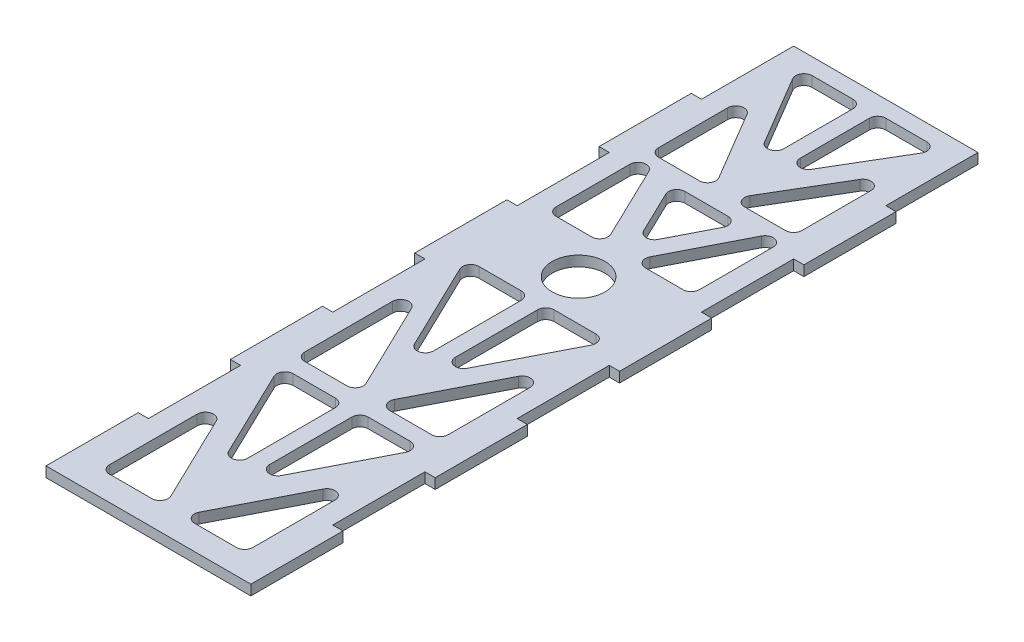
SolidWorks part; units mm, degrees
material "Balsa"
ref_plane "Front Plane" through (0, 0, 0) normal (0, 0, 1) x (1, 0, 0)
ref_plane "Top Plane" through (0, 0, 0) normal (0, 1, 0) x (1, 0, 0)
ref_plane "Right Plane" through (0, 0, 0) normal (1, 0, 0) x (0, 0, -1)
sketch "Sketch1" plane through (0, -9.7437, 0) normal (0, 1, 0) x (1, 0, 0)
  line L0 (-31.75, 143.1759) -> (-28.575, 143.1759)
  line L1 (-28.575, 143.1759) -> (-28.575, 171.7509)
  line L2 (-28.575, 171.7509) -> (28.575, 171.7509)
  line L3 (28.575, 171.7509) -> (28.575, 143.1759)
  line L4 (28.575, 143.1759) -> (31.75, 143.1759)
  line L5 (31.75, 143.1759) -> (31.75, 114.6009)
  line L6 (31.75, 114.6009) -> (28.575, 114.6009)
  line L7 (28.575, 114.6009) -> (28.575, 86.0259)
  line L8 (28.575, 86.0259) -> (31.75, 86.0259)
  line L9 (31.75, 86.0259) -> (31.75, 57.4509)
  line L10 (31.75, 57.4509) -> (28.575, 57.4509)
  line L11 (28.575, 57.4509) -> (28.575, 28.8759)
  line L12 (28.575, 28.8759) -> (31.75, 28.8759)
  line L13 (31.75, 28.8759) -> (31.75, 0.3009)
  line L14 (31.75, 0.3009) -> (28.575, 0.3009)
  line L15 (28.575, 0.3009) -> (28.575, -28.2741)
  line L16 (28.575, -28.2741) -> (31.75, -28.2741)
  line L17 (31.75, -28.2741) -> (31.75, -56.8491)
  line L18 (31.75, -56.8491) -> (-31.75, -56.8491)
  line L19 (-31.75, -56.8491) -> (-31.75, -28.2741)
  line L20 (-31.75, -28.2741) -> (-28.575, -28.2741)
  line L21 (-28.575, -28.2741) -> (-28.575, 0.3009)
  line L22 (-28.575, 0.3009) -> (-31.75, 0.3009)
  line L23 (-31.75, 0.3009) -> (-31.75, 28.8759)
  line L24 (-31.75, 28.8759) -> (-28.575, 28.8759)
  line L25 (-28.575, 28.8759) -> (-28.575, 57.4509)
  line L26 (-28.575, 57.4509) -> (-31.75, 57.4509)
  line L27 (-31.75, 57.4509) -> (-31.75, 86.0259)
  line L28 (-31.75, 86.0259) -> (-28.575, 86.0259)
  line L29 (-28.575, 86.0259) -> (-28.575, 114.6009)
  line L30 (-28.575, 114.6009) -> (-31.75, 114.6009)
  line L31 (-31.75, 114.6009) -> (-31.75, 143.1759)
  line L71 (-17.7698, 166.6709) -> (-5.08, 166.6709)
  line L78 (-2.54, 164.1309) -> (-2.54, 142.6938)
  line L82 (-7.2658, 141.3999) -> (-19.9555, 162.837)
  line L83 (2.54, 164.1309) -> (2.54, 142.6938)
  line L84 (7.2658, 141.3999) -> (19.9555, 162.837)
  line L85 (17.7698, 166.6709) -> (5.08, 166.6709)
  line L86 (-22.225, 144.9279) -> (-22.225, 123.4909)
  line L87 (-19.685, 120.9509) -> (-6.9952, 120.9509)
  line L88 (-4.8095, 124.7847) -> (-17.4992, 146.2218)
  line L89 (4.8095, 124.7847) -> (17.4992, 146.2218)
  line L90 (22.225, 144.9279) -> (22.225, 123.4909)
  line L91 (19.685, 120.9509) -> (6.9952, 120.9509)
  line L98 (5.7498, 92.896) -> (17.4229, 115.756)
  line L99 (22.225, 114.6009) -> (22.225, 91.7409)
  line L100 (19.685, 89.2009) -> (8.0119, 89.2009)
  line L101 (-6.3727, 92.8442) -> (-17.3972, 115.7042)
  line L102 (-22.225, 114.6009) -> (-22.225, 91.7409)
  line L103 (-19.685, 89.2009) -> (-8.6606, 89.2009)
  line L104 (5.08, 63.8009) -> (18.076, 63.8009)
  line L105 (20.3381, 60.1057) -> (7.3421, 34.655)
  line L106 (2.54, 35.8101) -> (2.54, 61.2609)
  line L107 (-5.08, 63.8009) -> (-18.1801, 63.8009)
  line L108 (-20.468, 60.1575) -> (-7.3678, 32.9934)
  line L109 (-2.54, 34.0967) -> (-2.54, 61.2609)
  line L110 (17.4229, 40.4336) -> (4.4269, 14.9828)
  line L111 (6.689, 11.2877) -> (19.685, 11.2877)
  line L112 (22.225, 13.8277) -> (22.225, 39.2785)
  line L113 (-22.225, 40.9919) -> (-22.225, 13.8277)
  line L114 (-19.685, 11.2877) -> (-6.5849, 11.2877)
  line L115 (-4.297, 14.931) -> (-17.3972, 42.0952)
  line L116 (-18.1801, 6.2077) -> (-5.08, 6.2077)
  line L117 (-2.54, 3.6677) -> (-2.54, -23.4964)
  line L118 (-7.3678, -24.5998) -> (-20.468, 2.5644)
  line L122 (2.54, 3.6677) -> (2.54, -21.7831)
  line L123 (7.3421, -22.9382) -> (20.3381, 2.5126)
  line L124 (18.076, 6.2077) -> (5.08, 6.2077)
  line L131 (4.4269, -45.534) -> (17.4229, -20.0833)
  line L132 (22.225, -21.2384) -> (22.225, -46.6891)
  line L133 (19.685, -49.2291) -> (6.689, -49.2291)
  line L134 (-17.3972, -18.4217) -> (-4.297, -45.5858)
  line L135 (-6.5849, -49.2291) -> (-19.685, -49.2291)
  line L136 (-22.225, -46.6891) -> (-22.225, -19.525)
  line L137 (-28.575, 114.6009) -> (28.575, 114.6009) construction
  line L142 (6.8922, 115.8709) -> (-6.3828, 115.8709)
  line L143 (-8.6706, 112.2275) -> (-2.2228, 98.8575)
  line L144 (2.3272, 98.8057) -> (9.1544, 112.1757)
  arc A0 (-19.685, -49.2291) -> (-22.225, -46.6891) centre (-19.685, -46.6891) cw
  arc A1 (22.225, -46.6891) -> (19.685, -49.2291) centre (19.685, -46.6891) cw
  arc A2 (17.4229, -20.0833) -> (22.225, -21.2384) centre (19.685, -21.2384) cw
  arc A3 (-17.3972, -18.4217) -> (-22.225, -19.525) centre (-19.685, -19.525) ccw
  arc A4 (-4.297, -45.5858) -> (-6.5849, -49.2291) centre (-6.5849, -46.6891) cw
  arc A5 (4.4269, -45.534) -> (6.689, -49.2291) centre (6.689, -46.6891) ccw
  arc A6 (2.54, -21.7831) -> (7.3421, -22.9382) centre (5.08, -21.7831) ccw
  arc A7 (-2.54, -23.4964) -> (-7.3678, -24.5998) centre (-5.08, -23.4964) cw
  arc A8 (-18.1801, 6.2077) -> (-20.468, 2.5644) centre (-18.1801, 3.6677) ccw
  arc A9 (-22.225, 13.8277) -> (-19.685, 11.2877) centre (-19.685, 13.8277) ccw
  arc A10 (-22.225, 40.9919) -> (-17.3972, 42.0952) centre (-19.685, 40.9919) cw
  arc A11 (-6.5849, 11.2877) -> (-4.297, 14.931) centre (-6.5849, 13.8277) ccw
  arc A12 (-5.08, 6.2077) -> (-2.54, 3.6677) centre (-5.08, 3.6677) cw
  arc A13 (2.54, 3.6677) -> (5.08, 6.2077) centre (5.08, 3.6677) cw
  arc A14 (20.3381, 2.5126) -> (18.076, 6.2077) centre (18.076, 3.6677) ccw
  arc A15 (19.685, 11.2877) -> (22.225, 13.8277) centre (19.685, 13.8277) ccw
  arc A16 (4.4269, 14.9828) -> (6.689, 11.2877) centre (6.689, 13.8277) ccw
  arc A17 (17.4229, 40.4336) -> (22.225, 39.2785) centre (19.685, 39.2785) cw
  arc A18 (18.076, 63.8009) -> (20.3381, 60.1057) centre (18.076, 61.2609) cw
  arc A19 (5.08, 63.8009) -> (2.54, 61.2609) centre (5.08, 61.2609) ccw
  arc A20 (7.3421, 34.655) -> (2.54, 35.8101) centre (5.08, 35.8101) cw
  arc A21 (-7.3678, 32.9934) -> (-2.54, 34.0967) centre (-5.08, 34.0967) ccw
  arc A22 (-5.08, 63.8009) -> (-2.54, 61.2609) centre (-5.08, 61.2609) cw
  arc A23 (-18.1801, 63.8009) -> (-20.468, 60.1575) centre (-18.1801, 61.2609) ccw
  arc A24 (-22.225, 91.7409) -> (-19.685, 89.2009) centre (-19.685, 91.7409) ccw
  arc A25 (-17.3972, 115.7042) -> (-22.225, 114.6009) centre (-19.685, 114.6009) ccw
  arc A26 (-6.3727, 92.8442) -> (-8.6606, 89.2009) centre (-8.6606, 91.7409) cw
  arc A27 (5.7498, 92.896) -> (8.0119, 89.2009) centre (8.0119, 91.7409) ccw
  arc A28 (22.225, 91.7409) -> (19.685, 89.2009) centre (19.685, 91.7409) cw
  arc A29 (17.4229, 115.756) -> (22.225, 114.6009) centre (19.685, 114.6009) cw
  arc A36 (-22.225, 123.4909) -> (-19.685, 120.9509) centre (-19.685, 123.4909) ccw
  arc A37 (-22.225, 144.9279) -> (-17.4992, 146.2218) centre (-19.685, 144.9279) cw
  arc A38 (-6.9952, 120.9509) -> (-4.8095, 124.7847) centre (-6.9952, 123.4909) ccw
  arc A39 (4.8095, 124.7847) -> (6.9952, 120.9509) centre (6.9952, 123.4909) ccw
  arc A40 (22.225, 123.4909) -> (19.685, 120.9509) centre (19.685, 123.4909) cw
  arc A41 (17.4992, 146.2218) -> (22.225, 144.9279) centre (19.685, 144.9279) cw
  arc A42 (2.54, 164.1309) -> (5.08, 166.6709) centre (5.08, 164.1309) cw
  arc A43 (17.7698, 166.6709) -> (19.9555, 162.837) centre (17.7698, 164.1309) cw
  arc A44 (2.54, 142.6938) -> (7.2658, 141.3999) centre (5.08, 142.6938) ccw
  arc A45 (-2.54, 142.6938) -> (-7.2658, 141.3999) centre (-5.08, 142.6938) cw
  arc A46 (-5.08, 166.6709) -> (-2.54, 164.1309) centre (-5.08, 164.1309) cw
  arc A47 (-17.7698, 166.6709) -> (-19.9555, 162.837) centre (-17.7698, 164.1309) ccw
  circle A52 centre (0, 76.5009) radius 8.1915
  arc A53 (-6.3828, 115.8709) -> (-8.6706, 112.2275) centre (-6.3828, 113.3309) ccw
  arc A54 (-2.2228, 98.8575) -> (2.3272, 98.8057) centre (0.065, 99.9608) ccw
  arc A55 (6.8922, 115.8709) -> (9.1544, 112.1757) centre (6.8922, 113.3309) cw
  point P75 (0, 171.7509)
  point P116 (0, 94.2482)
  point P131 (-2.54, -49.2291)
  point P134 (2.54, -49.2291)
  point P141 (-22.225, 6.2077)
  point P148 (-2.54, 11.2877)
  point P155 (22.225, 6.2077)
  point P160 (2.54, 11.2877)
  point P165 (22.225, 63.8009)
  point P168 (2.54, 63.8009)
  point P177 (-22.225, 63.8009)
  point P184 (-4.6157, 89.2009)
  point P187 (3.8629, 89.2009)
  point P213 (-2.54, 120.9509)
  point P216 (2.54, 120.9509)
  point P225 (22.225, 166.6709)
  point P234 (-22.225, 166.6709)
  dimension "D16" = 2.54
  dimension "D17" = 6.35
  dimension "D21" = 2.54
  dimension "D27" = 2.54
  dimension "D5" = 16.383
  dimension "D1" = 6.35
  dimension "D2" = 6.35
  dimension "D3" = 5.08
  dimension "D4" = 6.35
  dimension "D6" = 5.08
  dimension "D7" = 6.35
  dimension "D8" = 5.08
  dimension "D9" = 6.35
  dimension "D10" = 12.7
  dimension "D11" = 25.4
  dimension "D12" = 5.08
  dimension "D13" = 7.62
  dimension "D14" = 29.21
  dimension "D15" = 63.5
  dimension "D18" = 6.35
  dimension "D19" = 5.08
  dimension "D20" = 6.35
  dimension "D22" = 45.72
  dimension "D23" = 31.75
  dimension "D24" = 26.035
  dimension "D25" = 26.035
  dimension "D26" = 6.35
extrude "Boss-Extrude1" add sketch "Sketch1" along normal blind 3.175
